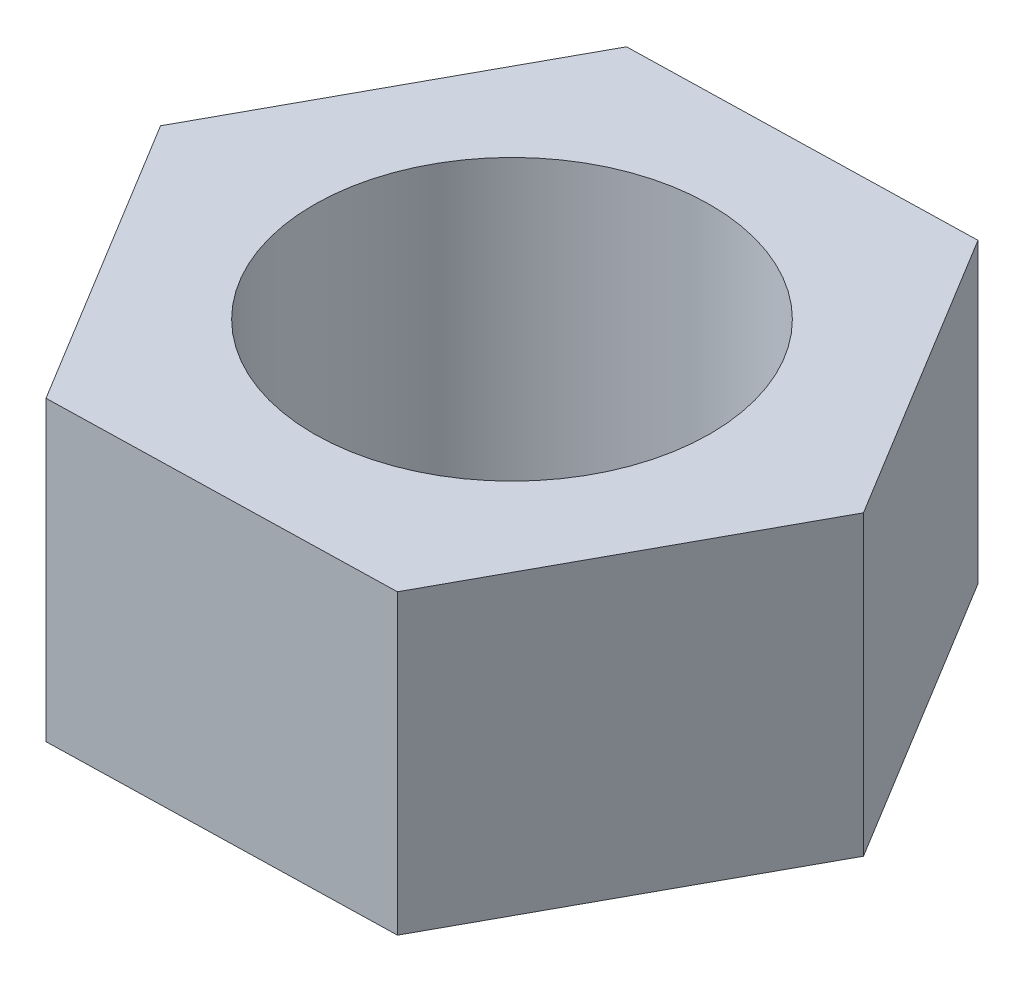
SolidWorks part; units mm, degrees
ref_plane "Alzado" through (0, 0, 0) normal (0, 0, 1) x (1, 0, 0)
ref_plane "Planta" through (0, 0, 0) normal (0, 1, 0) x (1, 0, 0)
ref_plane "Vista lateral" through (0, 0, 0) normal (1, 0, 0) x (0, 0, -1)
sketch "Croquis1" plane through (0, 0, 0) normal (0, 1, 0) x (1, 0, 0)
  line L1 (-13.8525, -0.3288) -> (-6.6415, -12.161)
  line L2 (-6.6415, -12.161) -> (7.211, -11.8322)
  line L3 (7.211, -11.8322) -> (13.8525, 0.3288)
  line L4 (13.8525, 0.3288) -> (6.6415, 12.161)
  line L5 (6.6415, 12.161) -> (-7.211, 11.8322)
  line L6 (-7.211, 11.8322) -> (-13.8525, -0.3288)
  circle A0 centre (0, 0) radius 8
  circle A1 centre (0, 0) radius 12 construction
  dimension "D1" = 16
  dimension "D2" = 24
extrude "Saliente-Extruir1" add sketch "Croquis1" along normal blind 12
